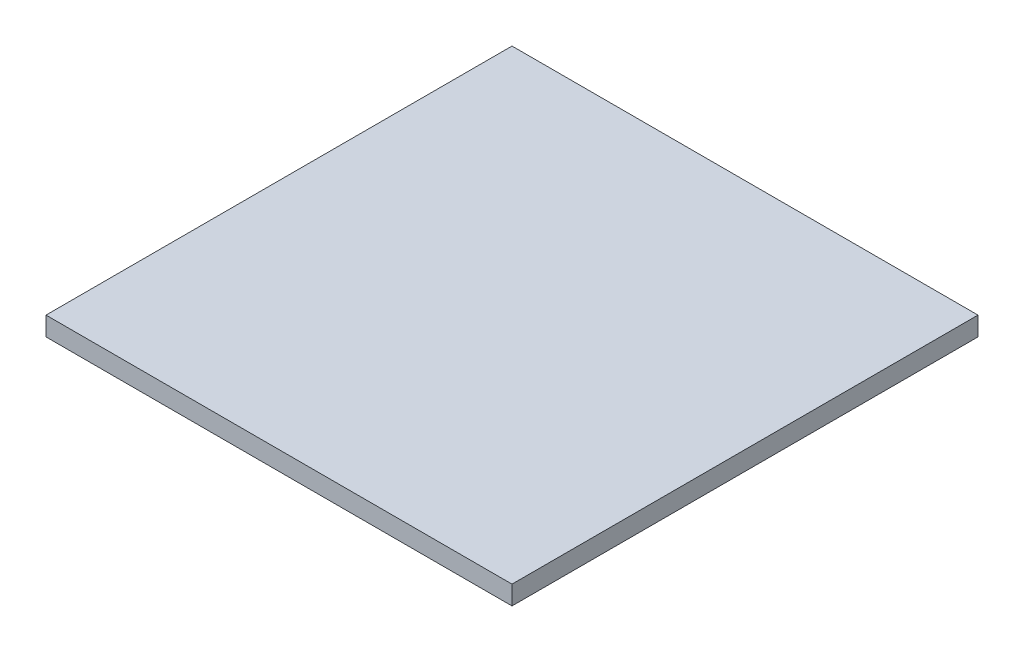
SolidWorks part; units mm, degrees
ref_plane "前视基准面" through (0, 0, 0) normal (0, 0, 1) x (1, 0, 0)
ref_plane "上视基准面" through (0, 0, 0) normal (0, 1, 0) x (1, 0, 0)
ref_plane "右视基准面" through (0, 0, 0) normal (1, 0, 0) x (0, 0, -1)
sketch "草图1" plane through (0, 0, 0) normal (0, 1, 0) x (1, 0, 0)
  line L1 (-25, -25) -> (25, -25)
  line L2 (-25, -25) -> (-25, 25)
  line L3 (-25, 25) -> (25, 25)
  line L4 (25, -25) -> (25, 25)
  line L5 (-25, -25) -> (25, 25) construction
  line L6 (-25, 25) -> (25, -25) construction
  point P0 (0, 0)
  dimension "D1" = 50
  dimension "D2" = 50
extrude "凸台-拉伸1" add sketch "草图1" along normal blind 2.03
